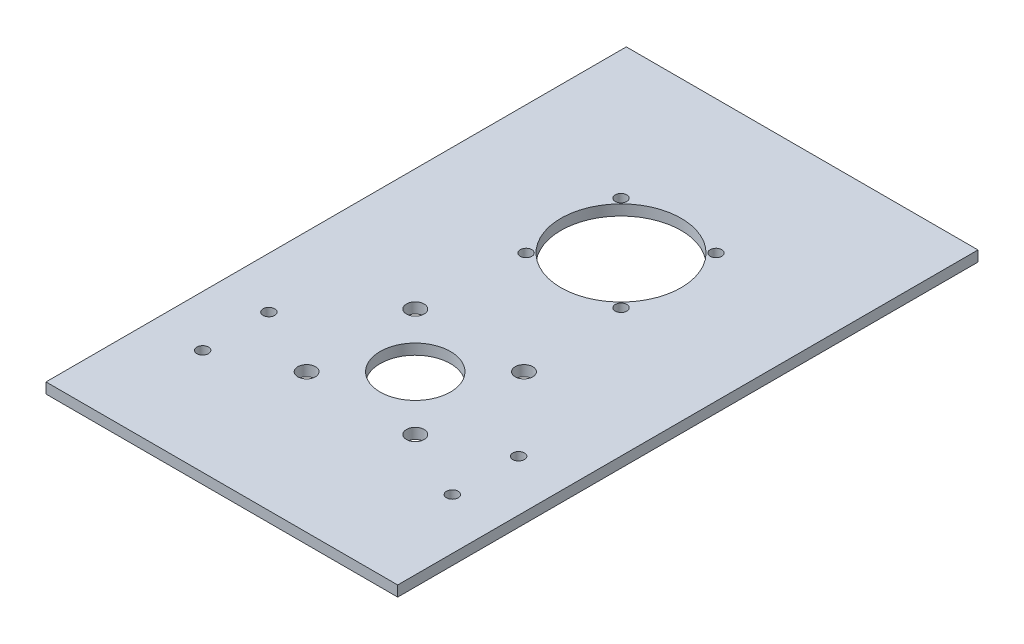
SolidWorks part; units mm, degrees
ref_plane "Front Plane" through (0, 0, 0) normal (0, 0, 1) x (1, 0, 0)
ref_plane "Top Plane" through (0, 0, 0) normal (0, 1, 0) x (1, 0, 0)
ref_plane "Right Plane" through (0, 0, 0) normal (1, 0, 0) x (0, 0, -1)
sketch "Croquis1" plane through (0, 0, 0) normal (0, 1, 0) x (1, 0, 0)
  line L1 (-50, 82.5) -> (50, 82.5)
  line L2 (-50, 82.5) -> (-50, -82.5)
  line L3 (-50, -82.5) -> (50, -82.5)
  line L4 (50, 82.5) -> (50, -82.5)
  line L5 (-50, 82.5) -> (50, -82.5) construction
  line L6 (-50, -82.5) -> (50, 82.5) construction
  circle A0 centre (0, -27.5) radius 10
  circle A1 centre (0, 31) radius 17.1
  circle A2 centre (-15.45, -42.95) radius 2.5
  circle A3 centre (15.45, -42.95) radius 2.5
  circle A4 centre (15.45, -12.05) radius 2.5
  circle A5 centre (-15.45, -12.05) radius 2.5
  circle A6 centre (-13.5, 17.5) radius 1.65
  circle A7 centre (13.5, 17.5) radius 1.65
  circle A8 centre (13.5, 44.5) radius 1.65
  circle A9 centre (-13.5, 44.5) radius 1.65
  circle A10 centre (35.5, -33.6222) radius 1.65
  circle A11 centre (35.5, -52.4648) radius 1.65
  circle A12 centre (-35.5, -52.4648) radius 1.65
  circle A13 centre (-35.5, -33.6222) radius 1.65
  point P0 (0, 0)
  dimension "D3" = 20
  dimension "D4" = 34.2
  dimension "D7" = 5
  dimension "D1" = 100
  dimension "D2" = 165
  dimension "D5" = 55
  dimension "D6" = 58.5
  dimension "D8" = 15.45
  dimension "D9" = 15.45
  dimension "D10" = 15.45
  dimension "D11" = 15.45
extrude "Saliente-Extruir1" add sketch "Croquis1" along normal blind 3
